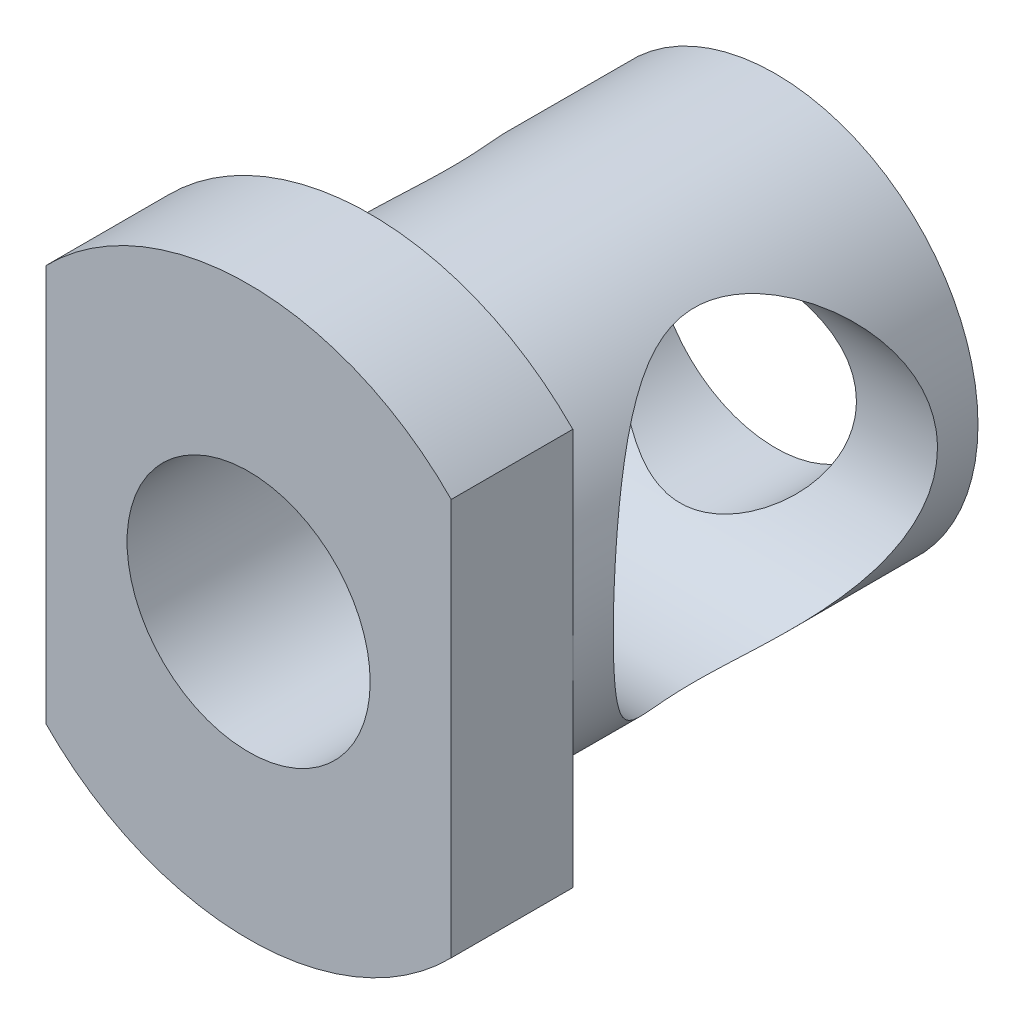
SolidWorks part; units mm, degrees
ref_plane "前视基准面" through (0, 0, 0) normal (0, 0, 1) x (1, 0, 0)
ref_plane "上视基准面" through (0, 0, 0) normal (0, 1, 0) x (1, 0, 0)
ref_plane "右视基准面" through (0, 0, 0) normal (1, 0, 0) x (0, 0, -1)
sketch "草图1" plane through (0, 0, 0) normal (0, 0, 1) x (1, 0, 0)
  circle A0 centre (0, 0) radius 2.5
extrude "凸台-拉伸1" add sketch "草图1" along normal blind 5
sketch "草图2" plane through (0, 0, 5) normal (0, 0, 1) x (1, 0, 0)
  line L0 (-2.5, 2.4495) -> (-2.5, -2.4495)
  line L2 (2.5, 2.4495) -> (2.5, -2.4495)
  arc A0 (-2.5, -2.4495) -> (2.5, -2.4495) centre (0, 0) ccw
  arc A1 (2.5, 2.4495) -> (-2.5, 2.4495) centre (0, 0) ccw
extrude "凸台-拉伸2" add sketch "草图2" along normal blind 1.5
sketch "草图3" plane through (0, 0, 6.5) normal (0, 0, 1) x (1, 0, 0)
  circle A0 centre (0, 0) radius 1.5
  dimension "D1" = 3
extrude "切除-拉伸1" cut sketch "草图3" against normal through all
sketch "草图4" plane through (0, 0, 0) normal (1, 0, 0) x (0, 0, -1)
  line L0 (0, 0) -> (-2.5, 0) construction
  circle A0 centre (-2.5, 0) radius 2
  dimension "D1" = 2.5
extrude "切除-拉伸2" cut sketch "草图4" against normal mid plane 10
